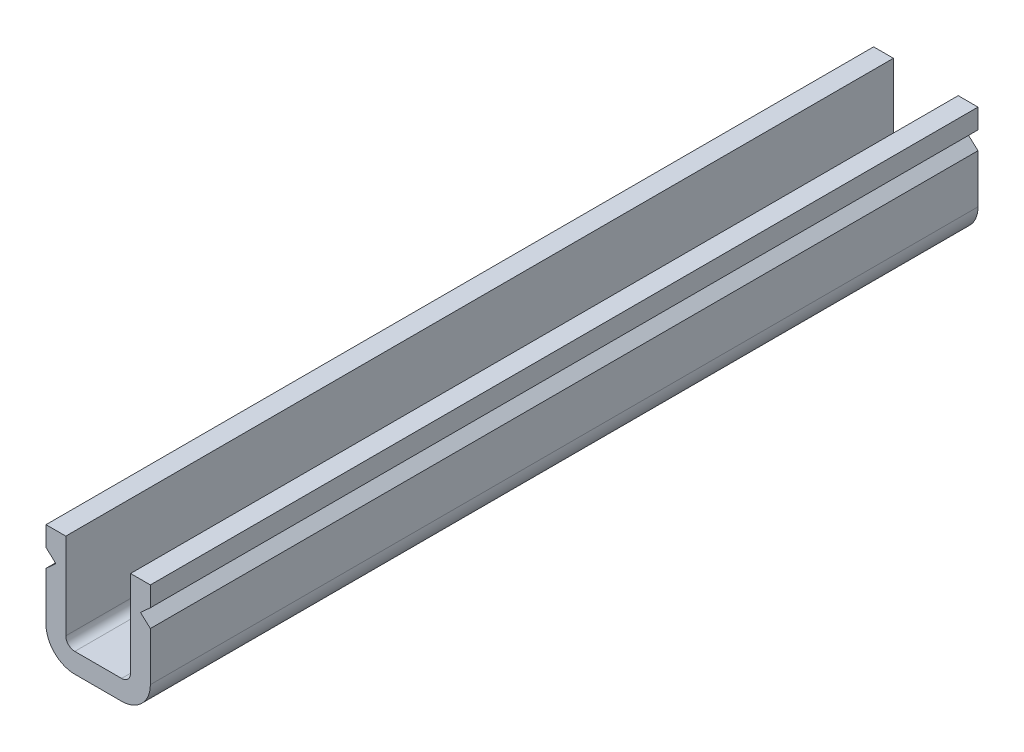
SolidWorks part; units mm, degrees
ref_plane "Plan de face" through (0, 0, 0) normal (0, 0, 1) x (1, 0, 0)
ref_plane "Plan de dessus" through (0, 0, 0) normal (0, 1, 0) x (1, 0, 0)
ref_plane "Plan de droite" through (0, 0, 0) normal (1, 0, 0) x (0, 0, -1)
sketch "Esquisse1" plane through (0, 0, 0) normal (0, 0, 1) x (1, 0, 0)
  line L0 (0, 0) -> (5.8, 0) construction
  line L1 (0, -1.1) -> (5.8, -1.1) construction
  line L2 (0.55, -1.6) -> (5.25, -1.6) construction
  line L3 (0, -2.1) -> (5.8, -2.1) construction
  line L4 (4.7, -4.8) -> (4.7, 0)
  line L22 (5.8, -1.1) -> (5.8, 0)
  line L23 (5.8, -2.1) -> (5.25, -1.6)
  line L24 (0, 0) -> (0, -1.1)
  line L25 (1.6, -6.4) -> (4.2, -6.4)
  line L26 (5.8, -4.8) -> (5.8, -2.1)
  line L27 (5.8, 0) -> (4.7, 0)
  line L28 (5.8, -1.1) -> (5.25, -1.6)
  line L29 (4.7, -5.3) -> (4.7, -2.5866) construction
  line L30 (1.1, -1.1) -> (1.1, -5.3) construction
  line L31 (1.1, 0) -> (0, 0)
  line L32 (5.8, 0) -> (0, 0) construction
  line L33 (1.1, 0) -> (1.1, -4.8)
  line L34 (1.6, -5.3) -> (4.2, -5.3)
  line L35 (4.7, -2.5866) -> (3.6147, -1.6) construction
  line L36 (4.1647, -1.1) -> (3.6147, -1.6) construction
  line L37 (4.1647, -1.1) -> (1.1, -1.1) construction
  line L38 (4.1647, -1.1) -> (4.1647, -1.1) construction
  line L39 (1.1, -5.3) -> (4.7, -5.3) construction
  line L40 (0, -1.1) -> (0.55, -1.6)
  line L41 (0, -2.1) -> (0.55, -1.6)
  line L42 (0, -2.1) -> (0, -4.8)
  line L43 (0, 0) -> (0, -6.4) construction
  line L44 (0, -6.4) -> (5.8, -6.4) construction
  line L45 (5.8, -6.4) -> (5.8, -2.1) construction
  arc A0 (1.1, -4.8) -> (1.6, -5.3) centre (1.6, -4.8) ccw
  arc A5 (4.7, -4.8) -> (4.2, -5.3) centre (4.2, -4.8) cw
  arc A6 (0, -4.8) -> (1.6, -6.4) centre (1.6, -4.8) ccw
  arc A7 (4.2, -6.4) -> (5.8, -4.8) centre (4.2, -4.8) ccw
  dimension "D2" = 0.5
  dimension "D3" = 1.1
  dimension "D4" = 1.6
  dimension "D9" = 0.5
  dimension "D1" = 1.1
  dimension "D5" = 2.7
  dimension "D6" = 4.8
  dimension "D7" = 2.6
  dimension "D8" = 0.55
  dimension "D10" = 0.55
extrude "Extrusion1" add sketch "Esquisse1" along normal blind 46
